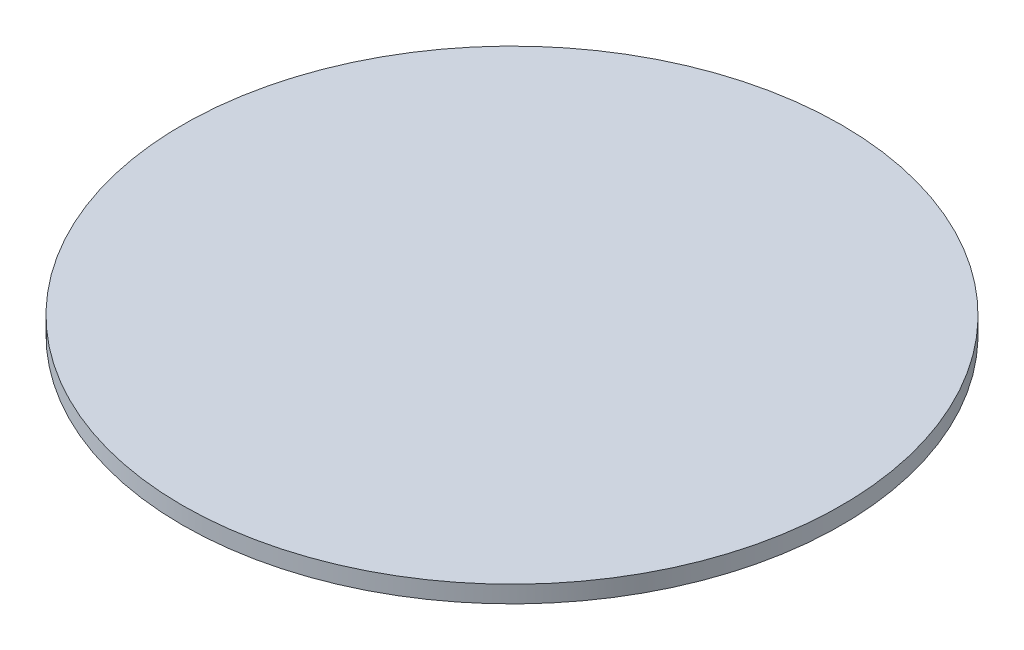
SolidWorks part; units mm, degrees
material "Glass"
ref_plane "Front Plane" through (0, 0, 0) normal (0, 0, 1) x (1, 0, 0)
ref_plane "Top Plane" through (0, 0, 0) normal (0, 1, 0) x (1, 0, 0)
ref_plane "Right Plane" through (0, 0, 0) normal (1, 0, 0) x (0, 0, -1)
sketch "Эскиз1" plane through (0, 0, 0) normal (0, 1, 0) x (1, 0, 0)
  circle A0 centre (0, 0) radius 29
  dimension "D1" = 58
extrude "Бобышка-Вытянуть1" add sketch "Эскиз1" along normal blind 1.5
